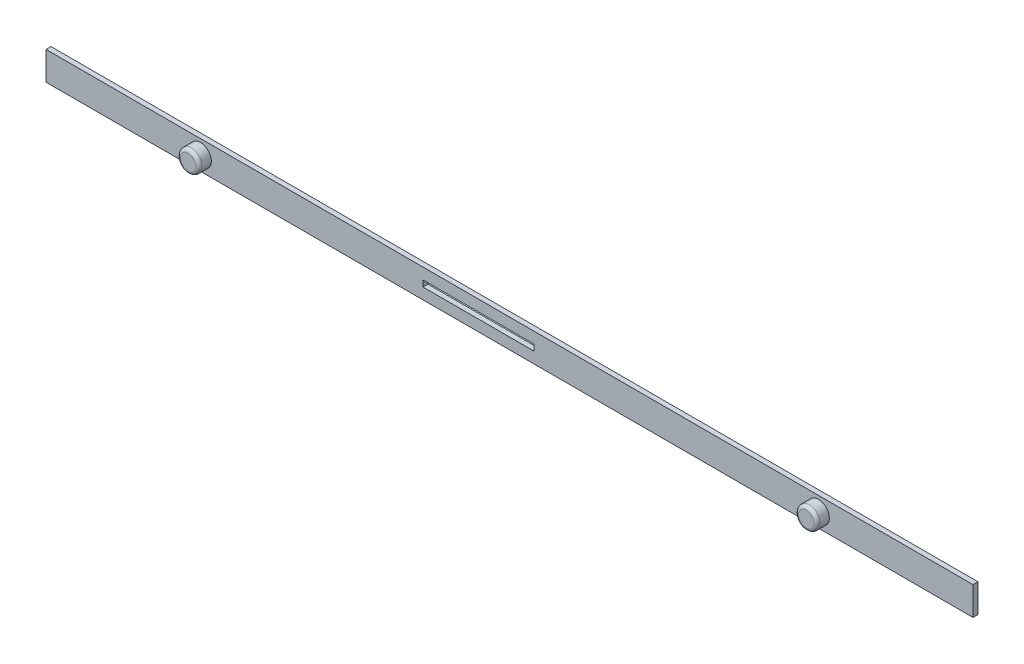
SolidWorks part; units mm, degrees
ref_plane "Přední rovina" through (0, 0, 0) normal (0, 0, 1) x (1, 0, 0)
ref_plane "Horní rovina" through (0, 0, 0) normal (0, 1, 0) x (1, 0, 0)
ref_plane "Pravá rovina" through (0, 0, 0) normal (1, 0, 0) x (0, 0, -1)
sketch "Skica2" plane through (0, 0, 0) normal (0, 0, 1) x (1, 0, 0)
  line L1 (-75, 2.3) -> (75, 2.3)
  line L2 (-75, 2.3) -> (-75, -2.3)
  line L3 (-75, -2.3) -> (75, -2.3)
  line L4 (75, 2.3) -> (75, -2.3)
  line L5 (-75, 2.3) -> (75, -2.3) construction
  line L6 (-75, -2.3) -> (75, 2.3) construction
  line L7 (4, 0.5) -> (-14, 0.5)
  line L8 (4, 0.5) -> (4, -0.5)
  line L9 (4, -0.5) -> (-14, -0.5)
  line L10 (-14, 0.5) -> (-14, -0.5)
  line L11 (4, 0.5) -> (-14, -0.5) construction
  line L12 (4, -0.5) -> (-14, 0.5) construction
  point P0 (0, 0)
  point P5 (-5, 0)
  dimension "D1" = 4.6
  dimension "D2" = 150
  dimension "D3" = 1
  dimension "D4" = 18
  dimension "D5" = 61
extrude "Přidat vysunutím2" add sketch "Skica2" along normal blind 0.8
sketch "Skica3" plane through (0, 0, 0.8) normal (0, 0, 1) x (1, 0, 0)
  line L0 (-75, 2.3) -> (-75, -2.3) construction
  line L1 (75, -2.3) -> (75, 2.3) construction
  line L2 (75, 2.3) -> (-75, 2.3) construction
  line L3 (-75, -2.3) -> (75, -2.3) construction
  circle A0 centre (-50, 0) radius 1.75
  circle A1 centre (50, 0) radius 1.75
  dimension "D1" = 3.5
  dimension "D3" = 3.5
  dimension "D2" = 25
  dimension "D4" = 25
  dimension "D5" = 2.3
  dimension "D6" = 2.3
extrude "Přidat vysunutím3" add sketch "Skica3" along normal blind 2
fillet "Zaoblit1" radius 0.5 2 edges at (51.75, 0, 2.8) (-48.25, 0, 2.8)
